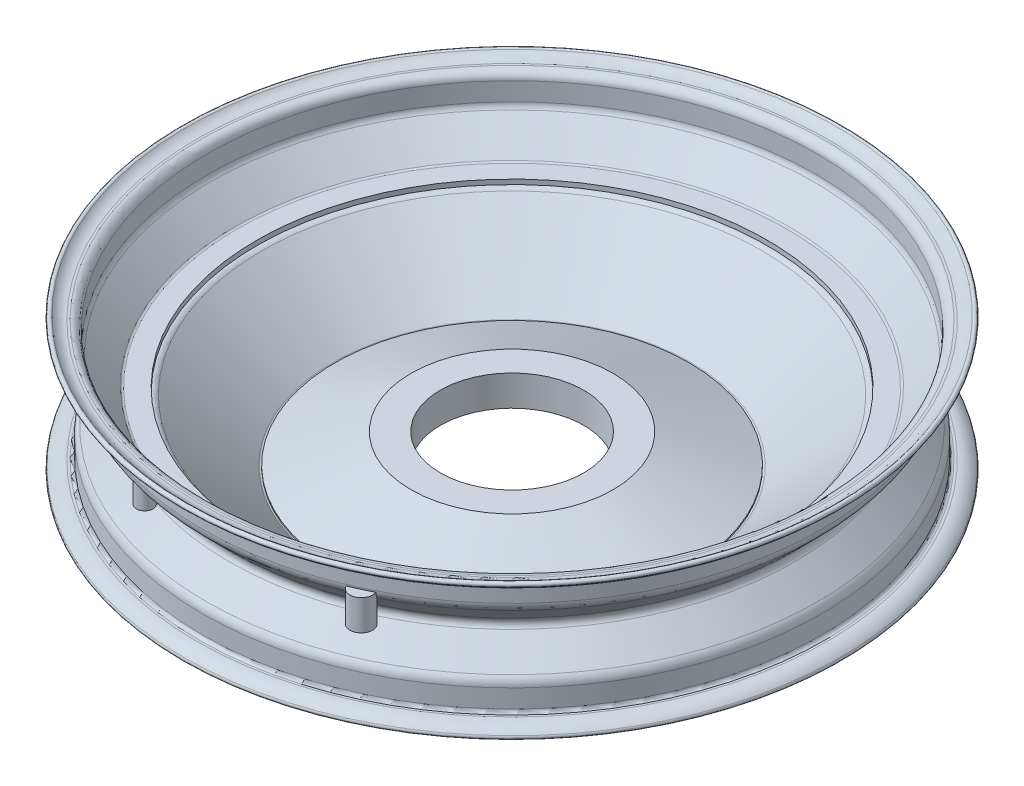
SolidWorks part; units mm, degrees
material "6061-T6 (SS)"
ref_plane "Front Plane" through (0, 0, 0) normal (0, 0, 1) x (1, 0, 0)
ref_plane "Top Plane" through (0, 0, 0) normal (0, 1, 0) x (1, 0, 0)
ref_plane "Right Plane" through (0, 0, 0) normal (1, 0, 0) x (0, 0, -1)
sketch "Sketch3" plane through (0, 0, 0) normal (0, 0, 1) x (1, 0, 0)
  line L0 (-167.2903, -3.118) -> (0, 0) construction
  line L1 (-102, -48.1245) -> (-116.0972, -48.1245)
  line L2 (-167.2903, -3.118) -> (-188.5358, -3.118) construction
  line L19 (-202.8572, -39.118) -> (-202.8572, -27.118)
  line L20 (-199.7392, -27.118) -> (-199.7392, -39.118)
  line L21 (-200.4193, -21.368) -> (-185.3526, -6.3013)
  line L22 (-181.4636, -6.8393) -> (-198.2515, -23.6091)
  line L23 (-199.7392, 20.882) -> (-199.7392, 32.882)
  line L24 (-202.8572, 32.882) -> (-202.8572, 20.882)
  line L25 (-204.8572, 38) -> (-206.3572, 38)
  line L26 (-206.3572, 34.882) -> (-204.8572, 34.882)
  line L27 (-200.4193, 15.132) -> (-185.3526, 0.0653)
  line L28 (-181.4638, 0.5856) -> (-198.2514, 17.3732)
  line L29 (-167.2903, -3.118) -> (-167.2903, 0)
  line L30 (-167.2903, 0) -> (-180.0494, 0)
  line L31 (-167.2903, -6.236) -> (-180.0494, -6.236)
  line L32 (-119.4407, -46.8814) -> (-165.9837, -6.7218)
  line L33 (-163.9468, -4.3611) -> (-117.4037, -44.5208)
  line L34 (-116.0972, -45.0065) -> (-102, -45.0065)
  line L35 (-102, -45.0065) -> (-102, -48.1245)
  line L38 (-204.8572, -44.236) -> (-206.3572, -44.236)
  line L39 (-206.3572, -41.118) -> (-204.8572, -41.118)
  line L41 (0, 240.889) -> (0, -99.5724) construction
  arc A1 (-185.3526, -6.3013) -> (-185.3526, 0.0653) centre (-188.5358, -3.118) ccw
  arc A18 (-204.8572, -41.118) -> (-202.8572, -39.118) centre (-204.8572, -39.118) ccw
  arc A19 (-204.8572, -44.236) -> (-199.7392, -39.118) centre (-204.8572, -39.118) ccw
  arc A20 (-200.4193, -21.368) -> (-202.8572, -27.118) centre (-194.8572, -27.118) ccw
  arc A21 (-198.2515, -23.6091) -> (-199.7392, -27.118) centre (-194.8572, -27.118) ccw
  arc A22 (-202.8572, 20.882) -> (-200.4193, 15.132) centre (-194.8572, 20.882) ccw
  arc A23 (-199.7392, 20.882) -> (-198.2514, 17.3732) centre (-194.8572, 20.8823) ccw
  arc A24 (-202.8572, 32.882) -> (-204.8572, 34.882) centre (-204.8572, 32.882) ccw
  arc A25 (-199.7392, 32.882) -> (-204.8572, 38) centre (-204.8572, 32.882) ccw
  arc A26 (-213.3101, 41.0829) -> (-215.6209, 38.9895) centre (-214.4655, 40.0362) ccw
  arc A27 (-213.3101, 41.0829) -> (-206.3572, 38) centre (-206.3572, 47.382) ccw
  arc A28 (-215.6209, 38.9895) -> (-206.3572, 34.882) centre (-206.3572, 47.382) ccw
  arc A29 (-181.4638, 0.5856) -> (-180.0494, 0) centre (-180.0497, 2) ccw
  arc A32 (-165.9837, -6.7218) -> (-167.2903, -6.236) centre (-167.2903, -8.236) ccw
  arc A33 (-163.9468, -4.3611) -> (-167.2903, -3.118) centre (-167.2903, -8.236) ccw
  arc A34 (-119.4407, -46.8814) -> (-116.0972, -48.1245) centre (-116.0972, -43.0065) ccw
  arc A35 (-117.4037, -44.5208) -> (-116.0972, -45.0065) centre (-116.0972, -43.0065) ccw
  arc A39 (-215.6209, -45.2255) -> (-213.3101, -47.3189) centre (-214.4655, -46.2722) ccw
  arc A40 (-206.3572, -44.236) -> (-213.3101, -47.3189) centre (-206.3572, -53.618) ccw
  arc A41 (-206.3572, -41.118) -> (-215.6209, -45.2255) centre (-206.3572, -53.618) ccw
  arc A43 (-180.0494, -6.236) -> (-181.4636, -6.8393) centre (-180.032, -8.2359) ccw
  dimension "D1" = 41.8885
  dimension "D5" = 4.5018
  dimension "D6" = 3.1178
  dimension "D2" = 76
  dimension "D3" = 3.118
  dimension "D4" = 3.118
  dimension "D7" = 179.969
revolve "Revolve2" add sketch "Sketch3" angle 360 about L41
sketch "Sketch4" plane through (0, 0, 0) normal (0, 1, 0) x (1, 0, 0)
  line L0 (0, 0) -> (0, 107) construction
  line L1 (0, 0) -> (-20.8747, 104.944) construction
  circle A0 centre (0, 107) radius 2.5
  circle A1 centre (-3884.1816, -9484.2438) radius 2.5
  circle A2 centre (-13412.7463, -13519.7463) radius 2.5
  circle A3 centre (-23003.9901, -9635.5647) radius 2.5
  circle A4 centre (-27039.4925, -107) radius 2.5
  circle A5 centre (-23155.3109, 9484.2438) radius 2.5
  circle A6 centre (-13626.7463, 13519.7463) radius 2.5
  circle A7 centre (-4035.5024, 9635.5647) radius 2.5
  circle A8 centre (-20.8747, 104.944) radius 2.5
  circle A9 centre (-3900.396, -9470.937) radius 2.5
  circle A10 centre (-13414.8022, -13498.8716) radius 2.5
  circle A11 centre (-22990.6833, -9619.3503) radius 2.5
  circle A12 centre (-27018.6178, -104.944) radius 2.5
  circle A13 centre (-23139.0965, 9470.937) radius 2.5
  circle A14 centre (-13624.6903, 13498.8716) radius 2.5
  circle A15 centre (-4048.8092, 9619.3503) radius 2.5
  circle A16 centre (75.6604, 75.6604) radius 2.5
  circle A17 centre (59.446, 88.9672) radius 2.5
  circle A18 centre (107, 0) radius 2.5
  circle A19 centre (104.944, 20.8747) radius 2.5
  circle A20 centre (75.6604, -75.6604) radius 2.5
  circle A21 centre (88.9672, -59.446) radius 2.5
  circle A22 centre (0, -107) radius 2.5
  circle A23 centre (20.8747, -104.944) radius 2.5
  circle A24 centre (-75.6604, -75.6604) radius 2.5
  circle A25 centre (-59.446, -88.9672) radius 2.5
  circle A26 centre (-107, 0) radius 2.5
  circle A27 centre (-104.944, -20.8747) radius 2.5
  circle A28 centre (-75.6604, 75.6604) radius 2.5
  circle A29 centre (-88.9672, 59.446) radius 2.5
  point P19 (-13519.7463, 0)
  point P37 (-13519.7463, 0)
  point P67 (0, 0)
  dimension "D1" = 107
  dimension "D2" = 5
  dimension "D4" = 11.25
  dimension "D5" = 8
  dimension "D3" = 8
  dimension "D6" = 8
extrude "Cut-Extrude3" cut sketch "Sketch4" against normal through all both and the other way through all
sketch "Sketch5" plane through (0, -45.0065, 0) normal (0, 1, 0) x (1, 0, 0)
  circle A0 centre (0, 0) radius 47
  circle A1 centre (0, 0) radius 116.0972 construction
  circle A2 centre (0, 0) radius 116.0972
  dimension "D1" = 94
extrude "Boss-Extrude1" add sketch "Sketch5" along normal blind 20
sketch "Sketch7" plane through (0, 0, 0) normal (0, 1, 0) x (1, 0, 0)
  circle A0 centre (-54.1396, -186.6351) radius 5.4102
  circle A1 centre (84.6799, -183.5502) radius 7.4037
extrude "Boss-Extrude2" add sketch "Sketch7" along normal blind 20
sketch "Sketch8" plane through (0, 0, 0) normal (1, 0, 0) x (0, 0, -1)
  line L0 (17.8185, -21.4713) -> (56.8926, -21.4713)
  line L1 (56.8926, -21.4713) -> (117.4037, -44.5208)
  line L3 (117.4037, -44.5208) -> (117.4037, 14.0962)
  line L4 (117.4037, 14.0962) -> (17.8185, 14.0962)
  line L5 (17.8185, 14.0962) -> (17.8185, -21.4713)
  point P0 (117.4037, -44.5208)
  point P4 (117.4037, -44.5208)
  point P5 (17.709, -23.0895)
  point P8 (116.0972, -35.0065)
  point P9 (0, 0)
  point P11 (17.8732, -23.4882)
revolve "Cut-Revolve1" cut sketch "Sketch8" angle 360 about L41
